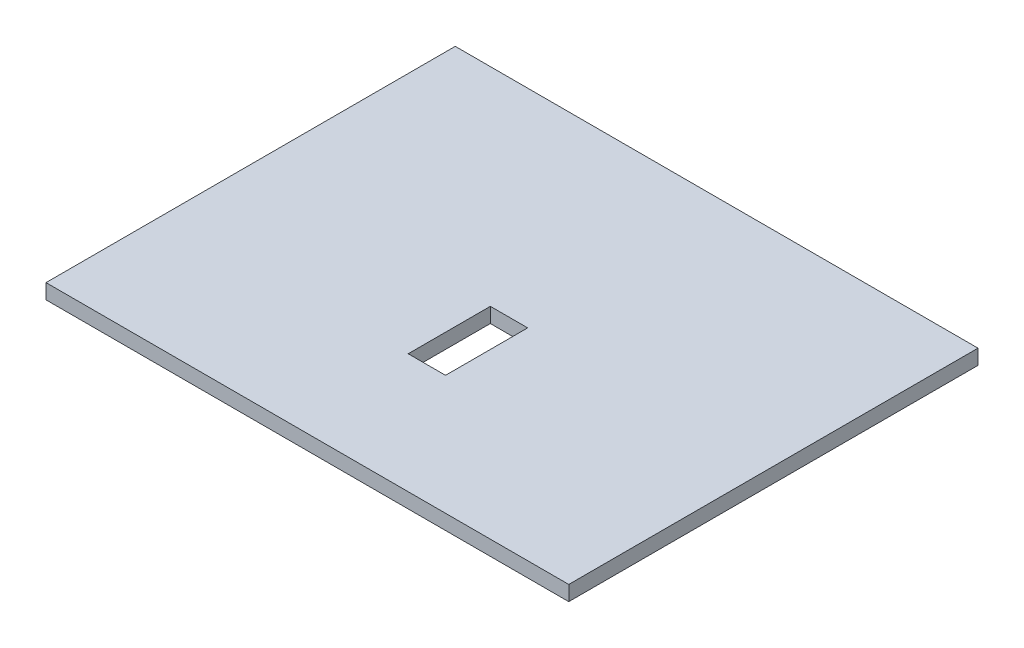
SolidWorks part; units mm, degrees
ref_plane "Front Plane" through (0, 0, 0) normal (0, 0, 1) x (1, 0, 0)
ref_plane "Top Plane" through (0, 0, 0) normal (0, 1, 0) x (1, 0, 0)
ref_plane "Right Plane" through (0, 0, 0) normal (1, 0, 0) x (0, 0, -1)
sketch "Sketch1" plane through (0, 0, 0) normal (0, 1, 0) x (1, 0, 0)
  line L1 (-175, -175) -> (175, -175)
  line L2 (-175, -175) -> (-175, 175)
  line L3 (-175, 175) -> (175, 175)
  line L4 (175, -175) -> (175, 175)
  line L5 (-175, -175) -> (175, 175) construction
  line L6 (-175, 175) -> (175, -175) construction
  point P0 (0, 0)
  dimension "D1" = 350
  dimension "D2" = 350
extrude "Boss-Extrude1" add sketch "Sketch1" along normal blind 10
sketch "Sketch2" plane through (0, 10, 0) normal (0, 1, 0) x (1, 0, 0)
  line L0 (-175, -175) -> (175, 175) construction
  line L1 (-175, 175) -> (175, -175) construction
  line L2 (0, 175) -> (0, -175) construction
  line L3 (175, 175) -> (-175, 175) construction
  line L4 (-175, -175) -> (175, -175) construction
  line L5 (-175, 0) -> (175, 0) construction
  line L6 (-175, 175) -> (-175, -175) construction
  line L7 (175, -175) -> (175, 175) construction
sketch "Sketch3" plane through (0, 10, 0) normal (0, 1, 0) x (1, 0, 0)
  line L0 (175, -175) -> (175, 175) construction
  line L1 (-175, -175) -> (175, -175)
  line L2 (-175, -175) -> (-175, -99)
  line L3 (-175, -99) -> (175, -99)
  line L4 (175, -175) -> (175, -99)
  dimension "D1" = 76
extrude "Cut-Extrude1" cut sketch "Sketch3" against normal blind 10
sketch "Sketch4" plane through (0, 10, 0) normal (0, 1, 0) x (1, 0, 0)
  line L0 (-175, -99) -> (175, 175) construction
  line L1 (-175, 175) -> (175, -99) construction
  line L2 (175, -99) -> (-175, -99) construction
  line L7 (-12.5, 36) -> (12.5, 36)
  line L8 (-12.5, 36) -> (-12.5, -19)
  line L9 (-12.5, -19) -> (12.5, -19)
  line L10 (12.5, 36) -> (12.5, -19)
  line L11 (-12.5, 36) -> (12.5, -19) construction
  line L12 (-12.5, -19) -> (12.5, 36) construction
  point P8 (0, 8.5)
  dimension "D1" = 25
  dimension "D2" = 55
  dimension "D3" = 80
extrude "Cut-Extrude2" cut sketch "Sketch4" against normal blind 10
